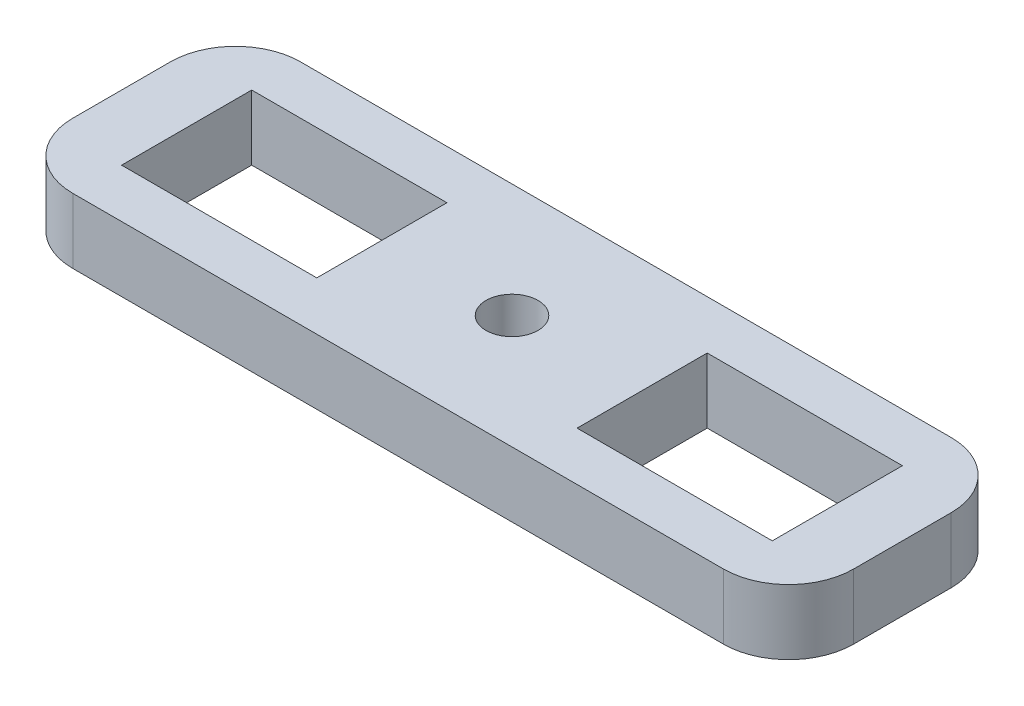
SolidWorks part; units mm, degrees
ref_plane "Front Plane" through (0, 0, 0) normal (0, 0, 1) x (1, 0, 0)
ref_plane "Top Plane" through (0, 0, 0) normal (0, 1, 0) x (1, 0, 0)
ref_plane "Right Plane" through (0, 0, 0) normal (1, 0, 0) x (0, 0, -1)
sketch "Sketch1" plane through (0, 0, 0) normal (0, 1, 0) x (1, 0, 0)
  line L0 (60, 0) -> (60, 75.4405) construction
  line L1 (0, 0) -> (120, 0) construction
  line L2 (0, 0) -> (0, 35) construction
  line L3 (0, 35) -> (120, 35) construction
  line L4 (120, 0) -> (120, 35) construction
  line L5 (0, 17.5) -> (131.1932, 17.5) construction
  line L6 (10, 27.5) -> (40, 27.5)
  line L7 (80, 27.5) -> (80, 7.5)
  line L8 (10, 27.5) -> (10, 7.5)
  line L9 (10, 7.5) -> (40, 7.5)
  line L10 (40, 27.5) -> (40, 7.5)
  line L11 (110, 7.5) -> (80, 7.5)
  line L12 (110, 27.5) -> (110, 7.5)
  line L13 (110, 27.5) -> (80, 27.5)
  line L15 (10, 0) -> (110, 0)
  line L16 (0, 10) -> (0, 25)
  line L17 (10, 35) -> (110, 35)
  line L18 (120, 10) -> (120, 25)
  circle A0 centre (60, 17.5) radius 4
  arc A1 (10, 0) -> (0, 10) centre (10, 10) cw
  arc A2 (0, 25) -> (10, 35) centre (10, 25) cw
  arc A3 (110, 35) -> (120, 25) centre (110, 25) cw
  arc A4 (110, 0) -> (120, 10) centre (110, 10) ccw
  point P9 (110, 17.5)
  point P14 (40, 17.5)
  point P15 (10, 17.5)
  point P16 (80, 17.5)
  dimension "D6" = 8
  dimension "D7" = 10
  dimension "D1" = 120
  dimension "D2" = 30
  dimension "D3" = 10
  dimension "D4" = 20
  dimension "D5" = 35
extrude "Boss-Extrude1" add sketch "Sketch1" along normal blind 10
